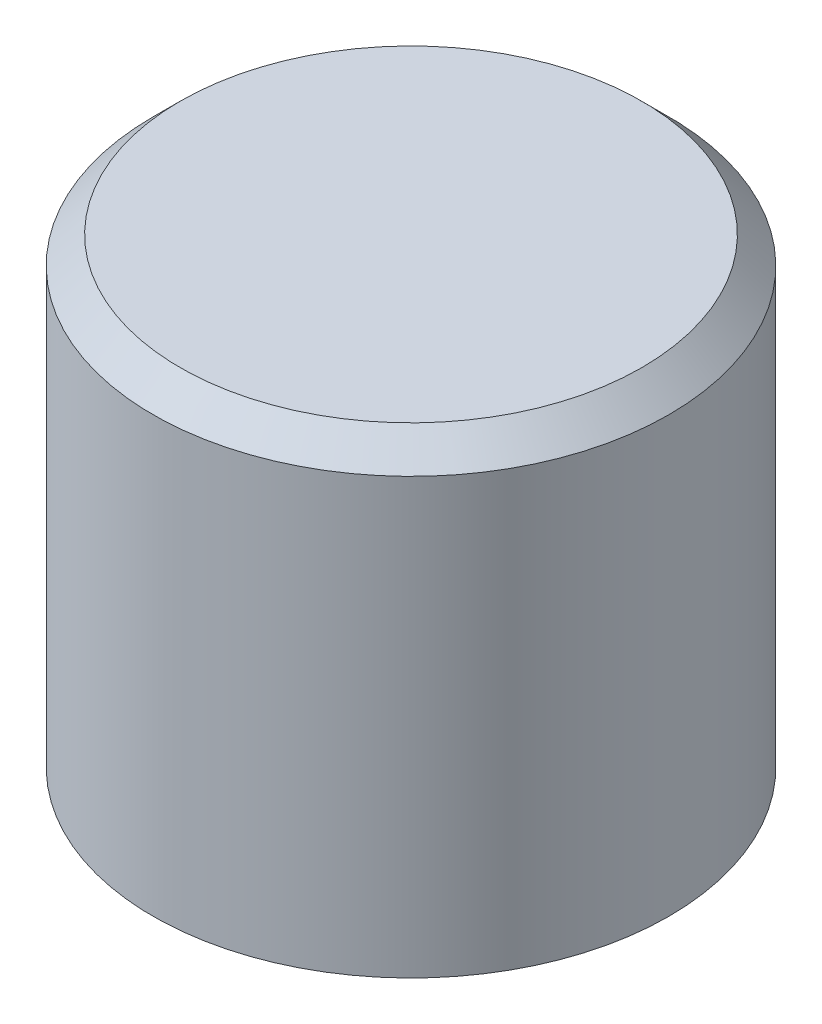
SolidWorks part; units mm, degrees
ref_plane "Front Plane" through (0, 0, 0) normal (0, 0, 1) x (1, 0, 0)
ref_plane "Top Plane" through (0, 0, 0) normal (0, 1, 0) x (1, 0, 0)
ref_plane "Right Plane" through (0, 0, 0) normal (1, 0, 0) x (0, 0, -1)
sketch "Sketch1" plane through (0, 0, 0) normal (0, 0, 1) x (1, 0, 0)
  line L0 (0, 8.5) -> (0, -8.5) construction
  line L1 (0, 8.5) -> (8.5, 8.5)
  line L2 (9.5, 7.5) -> (9.5, -8.5)
  line L3 (9.5, -8.5) -> (8.5, -8.5)
  line L4 (8.5, -8.5) -> (8.5, -3.5)
  line L7 (5.5, -0.5) -> (0, -0.5)
  line L8 (0, -0.5) -> (0, 8.5)
  line L12 (8.5, -3.5) -> (5.5, -0.5)
  line L13 (8.5, 8.5) -> (9.5, 7.5)
  point P3 (0, 0)
  point P8 (7.5, 6.5)
  point P9 (4, 6.5)
  point P10 (4, -0.5)
  point P14 (8.5, -0.5)
  point P17 (9.5, 8.5)
  dimension "D1" = 17
  dimension "D2" = 9.5
  dimension "D3" = 1
  dimension "D4" = 9
revolve "Revolve1" add sketch "Sketch1" angle 360 about L0
sketch "Sketch2" plane through (0, -0.5, 0) normal (0, -1, 0) x (1, 0, 0)
  circle A1 centre (0, 0) radius 3.175
  dimension "D1" = 6.35
extrude "Cut-Extrude1" cut sketch "Sketch2" against normal offset from surface (7 mm away) 2 up to face at (-8.5, 8.5, 0)
sketch "Sketch3" plane through (0, 0, 0) normal (0, 0, 1) x (1, 0, 0)
  line L1 (8.5, 8.5) -> (-8.5, 8.5) construction
  circle A0 centre (0, 2.5) radius 1.1303
  dimension "D1" = 2.2606
  dimension "D2" = 6
extrude "Cut-Extrude2" cut sketch "Sketch3" against normal up to surface (9.4325 mm away)
